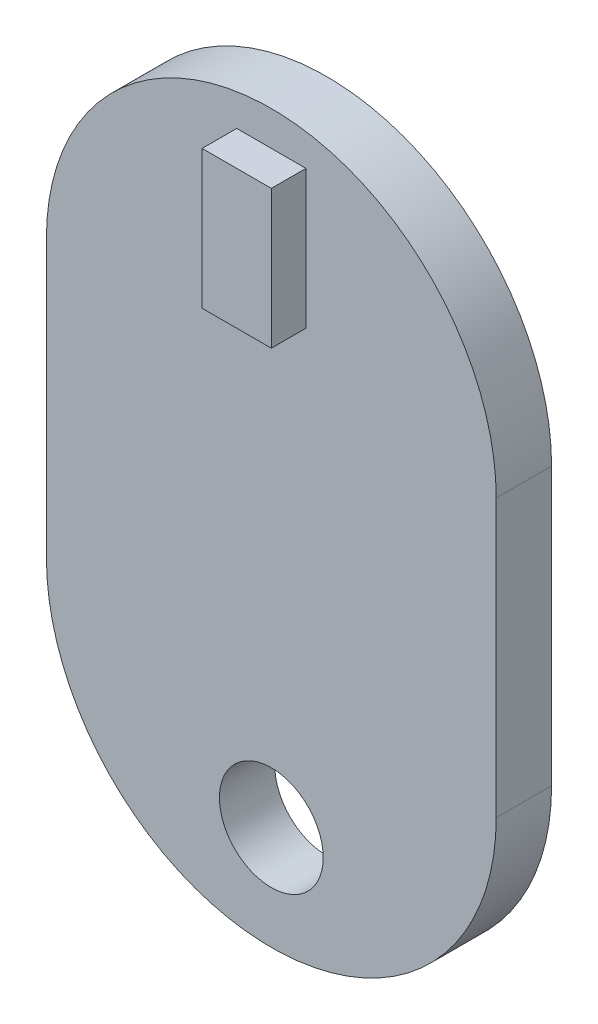
SolidWorks part; units mm, degrees
material "Fibre de verre A"
ref_plane "Plan de face" through (0, 0, 0) normal (0, 0, 1) x (1, 0, 0)
ref_plane "Plan de dessus" through (0, 0, 0) normal (0, 1, 0) x (1, 0, 0)
ref_plane "Plan de droite" through (0, 0, 0) normal (1, 0, 0) x (0, 0, -1)
sketch "Esquisse1" plane through (0, 0, 0) normal (0, 0, 1) x (1, 0, 0)
  line L0 (0, -3.5) -> (0, -11.5) construction
  line L1 (6.5, -3.5) -> (6.5, -11.5)
  line L2 (-6.5, -3.5) -> (-6.5, -11.5)
  arc A0 (6.5, -3.5) -> (-6.5, -3.5) centre (0, -3.5) ccw
  arc A1 (-6.5, -11.5) -> (6.5, -11.5) centre (0, -11.5) ccw
  circle A2 centre (0, -15) radius 1.5
  point P3 (0, -7.5)
  dimension "D2" = 21
  dimension "D4" = 3
  dimension "D1" = 13
  dimension "D3" = 3
  dimension "D5" = 3
extrude "Boss.-Extru.1" add sketch "Esquisse1" along normal blind 1.6
sketch "Esquisse2" plane through (0, 0, 1.6) normal (0, 0, 1) x (1, 0, 0)
  line L0 (-1, 2) -> (1, -2) construction
  line L1 (-1, 2) -> (1, 2)
  line L2 (-1, 2) -> (-1, -2)
  line L3 (-1, -2) -> (1, -2)
  line L4 (1, 2) -> (1, -2)
  dimension "D1" = 2
  dimension "D2" = 4
extrude "Boss.-Extru.2" add sketch "Esquisse2" along normal blind 1
sketch "Esquisse3" plane through (0, 0, 0) normal (1, 0, 0) x (0, 0, -1)
  line L0 (0, 0) -> (-21.7638, 0) construction
  line L1 (-1.6, 0) -> (-101.6, 0)
  line L2 (-101.6, 0) -> (-101.6, 22.1695)
  line L3 (-101.6, 22.1695) -> (-1.6, 0)
  line L4 (-1.6, -2) -> (-1.6, 2) construction
  dimension "D1" = 100
  dimension "D2" = 12.5
revolve "Révolution1" [suppressed] add sketch "Esquisse3" angle 360 about L0
